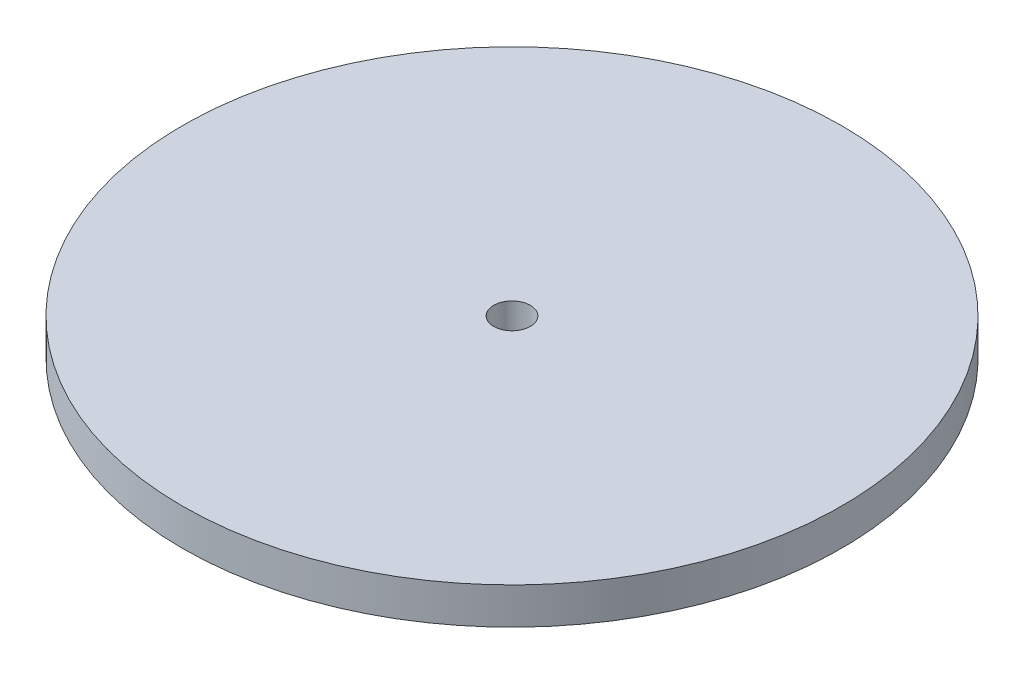
SolidWorks part; units mm, degrees
ref_plane "前视基准面" through (0, 0, 0) normal (0, 0, 1) x (1, 0, 0)
ref_plane "上视基准面" through (0, 0, 0) normal (0, 1, 0) x (1, 0, 0)
ref_plane "右视基准面" through (0, 0, 0) normal (1, 0, 0) x (0, 0, -1)
sketch "草图1" plane through (0, 0, 0) normal (0, 1, 0) x (1, 0, 0)
  circle A0 centre (0, 0) radius 90
extrude "凸台-拉伸1" add sketch "草图1" along normal blind 10 contours A0
sketch "草图2" plane through (0, 10, 0) normal (0, 1, 0) x (1, 0, 0)
  circle A0 centre (0, 0) radius 5
extrude "切除-拉伸1" cut sketch "草图2" against normal blind 10
